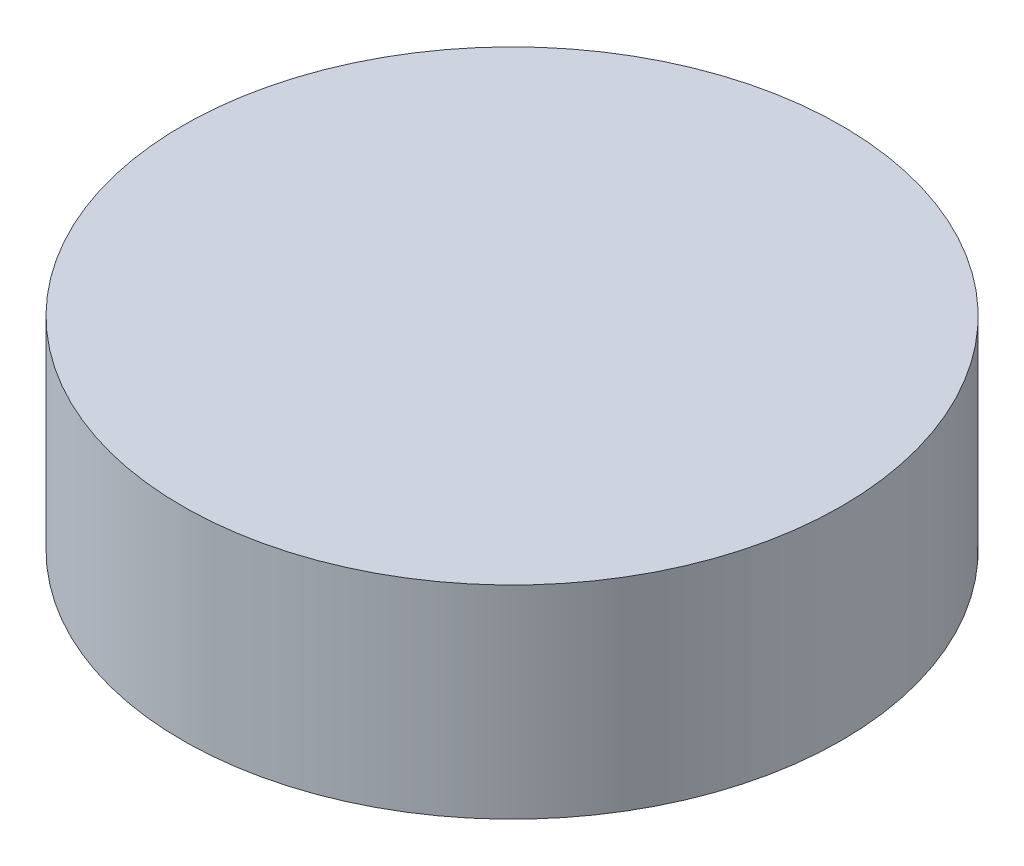
SolidWorks part; units mm, degrees
ref_plane "Alzado" through (0, 0, 0) normal (0, 0, 1) x (1, 0, 0)
ref_plane "Planta" through (0, 0, 0) normal (0, 1, 0) x (1, 0, 0)
ref_plane "Vista lateral" through (0, 0, 0) normal (1, 0, 0) x (0, 0, -1)
sketch "Croquis1" plane through (0, 0, 0) normal (0, 0, 1) x (1, 0, 0)
  circle A0 centre (0, 0) radius 16.51
  dimension "D1" = 33.02
extrude "Saliente-Extruir1" add sketch "Croquis1" along normal blind 10.16 contours A0
move or copy body "Corps-Déplacer/Copier1" bodies to move or copy 101 copy no rotation origin (0, 0, 0) rotation axis (1, 0, 0) rotation angle 90
